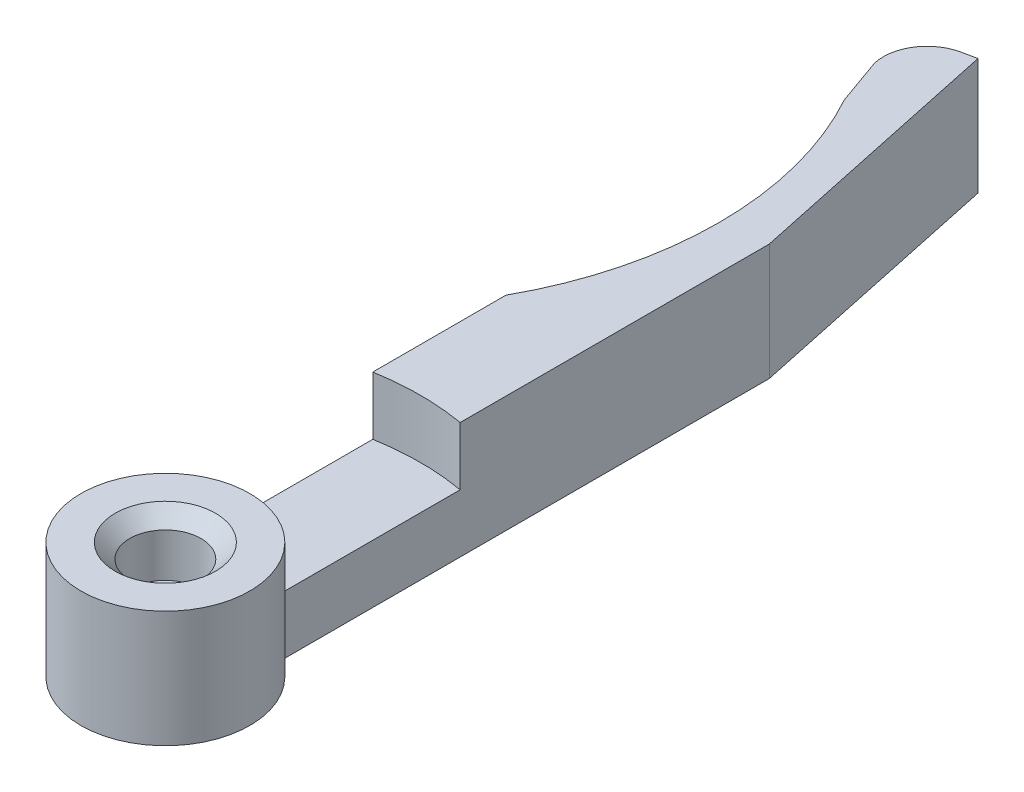
SolidWorks part; units mm, degrees
other "Marquage1"
sketch "Esquisse6" plane through (-5.8, 8, 5.8) normal (-0.828, 0.5586, 0.0482) x (0.5598, 0.8285, 0.0157)
ref_plane "Plan de face" through (0, 0, 0) normal (0, 0, 1) x (1, 0, 0)
ref_plane "Plan de dessus" through (0, 0, 0) normal (0, 1, 0) x (1, 0, 0)
ref_plane "Plan de droite" through (0, 0, 0) normal (1, 0, 0) x (0, 0, -1)
sketch "Esquisse1" plane through (0, 0, 0) normal (0, 1, 0) x (1, 0, 0)
  line L0 (-3, 50.619) -> (-3, 49.619) construction
  line L1 (2, 55.619) -> (3, 55.619) construction
  line L2 (-3, 55.619) -> (-3, 4.9639) construction
  line L3 (-3, 4.9639) -> (3, 4.9639) construction
  line L4 (3, 55.619) -> (3, 4.9639) construction
  line L5 (-3, 26.381) -> (-3, 4.9639)
  line L7 (-3, 4.9639) -> (3, 4.9639) construction
  line L12 (0, 4.9639) -> (0, -14.5149) construction
  line L13 (-4.1404, 52.822) -> (-3, 49.619)
  line L14 (-1.8453, 56.4495) -> (-0.8672, 56.6574)
  line L15 (-0.8672, 56.6574) -> (3, 38.4639)
  line L16 (3, 38.4639) -> (3, 4.9639)
  arc A0 (-3, 49.619) -> (-3, 26.381) centre (-24, 38) cw
  arc A1 (2, 55.619) -> (-3, 50.619) centre (2, 50.619) ccw construction
  circle A2 centre (0, 0) radius 2.4 construction
  arc A3 (-4.1404, 52.822) -> (-1.8453, 56.4495) centre (-1.2216, 53.5151) cw
  arc A4 (-3, 4.9639) -> (3, 4.9639) centre (0, 0) ccw
  point P19 (0, 38)
  point P25 (-4.3024, 55.9871)
  dimension "D2" = 24
  dimension "D5" = 5
  dimension "D10" = 3
  dimension "D7" = 4.8
  dimension "D11" = 5.8
  dimension "D1" = 6
  dimension "D3" = 21
  dimension "D4" = 6
  dimension "D6" = 38
  dimension "D8" = 3.5
  dimension "D9" = 6.5
  dimension "D12" = 33.5
  dimension "D13" = 12
  dimension "D14" = 18.6
  dimension "D15" = 3.4
  dimension "D16" = 1
extrude "Boss.-Extru.1" add sketch "Esquisse1" along normal blind 8
sketch "Esquisse2" plane through (0, 8, 0) normal (0, 1, 0) x (1, 0, 0)
  line L0 (0, 38) -> (0, 0) construction
  circle A0 centre (0, 0) radius 2.45
  arc A1 (-3, 26.381) -> (-3, 49.619) centre (-24, 38) ccw construction
  dimension "D2" = 4.9
  dimension "D1" = 38
extrude "Enlèv. mat.-Extru.1" cut sketch "Esquisse2" against normal blind 4
sketch "Esquisse3" plane through (0, 4, 0) normal (0, 1, 0) x (1, 0, 0)
  circle A0 centre (0, 0) radius 1.75
  dimension "D1" = 3.5
extrude "Enlèv. mat.-Extru.2" cut sketch "Esquisse3" against normal up to next
sketch "Esquisse4" plane through (0, 0, 0) normal (0, -1, 0) x (1, 0, 0)
  circle A0 centre (0, 0) radius 3.75
  dimension "D1" = 7.5
extrude "Enlèv. mat.-Extru.3" cut sketch "Esquisse4" against normal blind 2.5
sketch "Esquisse5" plane through (0, 8, 0) normal (0, 1, 0) x (1, 0, 0)
  line L0 (-3, 4.9639) -> (-3, 17.2409)
  line L1 (3, 4.9639) -> (3, 17.2409)
  line L2 (3, 4.9639) -> (3, 38.4639) construction
  circle A0 centre (0, 0) radius 5.8 construction
  circle A1 centre (0, 0) radius 17.5 construction
  arc A2 (-3, 4.9639) -> (3, 4.9639) centre (0, 0) ccw construction
  arc A3 (-3, 4.9639) -> (3, 4.9639) centre (0, 0) cw
  arc A4 (-3, 17.2409) -> (3, 17.2409) centre (0, 0) cw
  dimension "D1" = 35
extrude "Enlèv. mat.-Extru.4" cut sketch "Esquisse5" against normal blind 4
chamfer "Chanfrein1" distance 1 angle 45 1 edges at (0, 8, 2.45)
